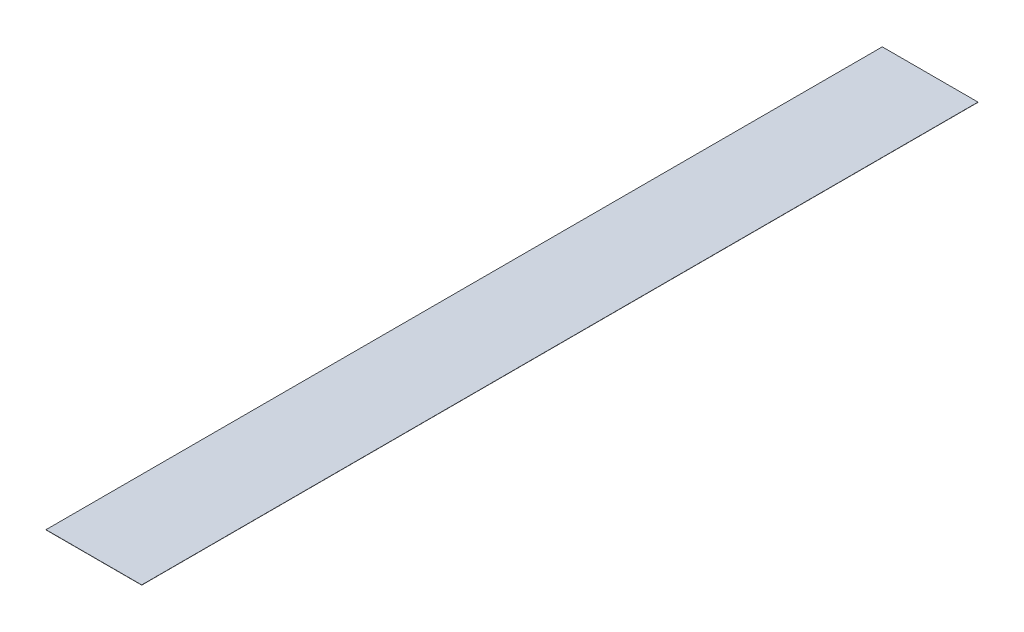
SolidWorks part; units mm, degrees
material "acrylic adhesive"
ref_plane "Front" through (0, 0, 0) normal (0, 0, 1) x (1, 0, 0)
ref_plane "Top" through (0, 0, 0) normal (0, 1, 0) x (1, 0, 0)
ref_plane "Right" through (0, 0, 0) normal (1, 0, 0) x (0, 0, -1)
sketch "Sketch1" plane through (0, 0, 0) normal (0, 1, 0) x (1, 0, 0)
  line L0 (-11.615, 101.495) -> (11.615, -101.495) construction
  line L1 (-11.615, 101.495) -> (11.615, 101.495)
  line L2 (-11.615, 101.495) -> (-11.615, -101.495)
  line L3 (-11.615, -101.495) -> (11.615, -101.495)
  line L4 (11.615, 101.495) -> (11.615, -101.495)
  point P4 (0, 0)
  dimension "D1" = 202.99
  dimension "D2" = 23.23
extrude "Extrude1" add sketch "Sketch1" along normal blind 0.0508
